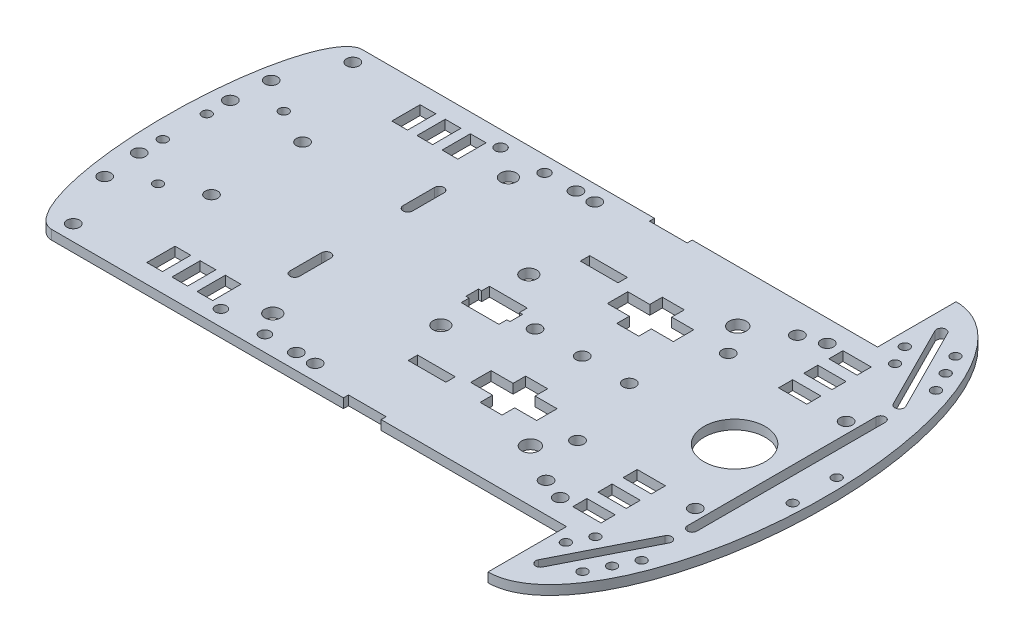
SolidWorks part; units mm, degrees
ref_plane "Front Plane" through (0, 0, 0) normal (0, 0, 1) x (1, 0, 0)
ref_plane "Top Plane" through (0, 0, 0) normal (0, 1, 0) x (1, 0, 0)
ref_plane "Right Plane" through (0, 0, 0) normal (1, 0, 0) x (0, 0, -1)
sketch "Sketch1" plane through (0, 0, 0) normal (0, 1, 0) x (1, 0, 0)
  line L1 (0, 0) -> (210, 0)
  line L2 (0, 0) -> (0, 149)
  line L3 (0, 149) -> (210, 149)
  line L4 (210, 0) -> (210, 149)
  dimension "D1" = 210
  dimension "D2" = 149
extrude "Boss-Extrude1" add sketch "Sketch1" along normal blind 3
sketch "Sketch2" plane through (0, 3, 0) normal (0, 1, 0) x (1, 0, 0)
  line L0 (210, 149) -> (0, 149) construction
  line L1 (177, 149) -> (0, 149)
  line L2 (177, 149) -> (177, 124)
  line L3 (177, 124) -> (0, 124)
  line L4 (0, 149) -> (0, 124)
  line L5 (0, 149) -> (0, 0) construction
  line L7 (0, 0) -> (177, 0)
  line L8 (0, 0) -> (0, 25)
  line L9 (0, 25) -> (177, 25)
  line L10 (177, 0) -> (177, 25)
  dimension "D1" = 177
  dimension "D2" = 25
  dimension "D3" = 25
extrude "Cut-Extrude1" cut sketch "Sketch2" against normal blind 3
sketch "Sketch3" plane through (0, 3, 0) normal (0, 1, 0) x (1, 0, 0)
  line L0 (0, 124) -> (177, 124) construction
  line L1 (143, 99.5) -> (122, 99.5)
  line L2 (143, 99.5) -> (143, 93)
  line L3 (143, 93) -> (122, 93)
  line L4 (122, 99.5) -> (122, 93)
  line L5 (129, 103.5) -> (136, 103.5)
  line L6 (129, 103.5) -> (129, 89)
  line L7 (129, 89) -> (136, 89)
  line L8 (136, 103.5) -> (136, 89)
  line L9 (177, 124) -> (177, 149) construction
  line L10 (118, 124) -> (106, 124)
  line L11 (118, 124) -> (118, 122.4)
  line L12 (118, 122.4) -> (106, 122.4)
  line L13 (106, 124) -> (106, 122.4)
  line L14 (210, 74.5) -> (0, 74.5) construction
  line L15 (118, 103.4) -> (106, 103.4)
  line L16 (118, 103.4) -> (118, 100.4)
  line L17 (118, 100.4) -> (106, 100.4)
  line L18 (106, 103.4) -> (106, 100.4)
  line L19 (181.5, 117.5) -> (172.5, 117.5)
  line L20 (181.5, 117.5) -> (181.5, 113)
  line L21 (181.5, 113) -> (172.5, 113)
  line L22 (172.5, 117.5) -> (172.5, 113)
  line L23 (172.5, 109.5) -> (181.5, 109.5)
  line L24 (172.5, 109.5) -> (172.5, 105)
  line L25 (172.5, 105) -> (181.5, 105)
  line L26 (181.5, 109.5) -> (181.5, 105)
  line L27 (172.5, 101.5) -> (181.5, 101.5)
  line L28 (172.5, 101.5) -> (172.5, 97)
  line L29 (172.5, 97) -> (181.5, 97)
  line L30 (181.5, 101.5) -> (181.5, 97)
  line L31 (210, 0) -> (210, 149) construction
  line L32 (0, 124) -> (0, 25) construction
  line L33 (181.5, 47.5) -> (181.5, 52)
  line L34 (172.5, 52) -> (181.5, 52)
  line L35 (172.5, 47.5) -> (172.5, 52)
  line L36 (172.5, 47.5) -> (181.5, 47.5)
  line L37 (181.5, 39.5) -> (181.5, 44)
  line L38 (172.5, 44) -> (181.5, 44)
  line L39 (172.5, 39.5) -> (172.5, 44)
  line L40 (172.5, 39.5) -> (181.5, 39.5)
  line L41 (172.5, 31.5) -> (172.5, 36)
  line L42 (181.5, 36) -> (172.5, 36)
  line L43 (181.5, 31.5) -> (181.5, 36)
  line L44 (181.5, 31.5) -> (172.5, 31.5)
  line L45 (106, 45.6) -> (106, 48.6)
  line L46 (118, 48.6) -> (106, 48.6)
  line L47 (118, 45.6) -> (118, 48.6)
  line L48 (118, 45.6) -> (106, 45.6)
  line L49 (106, 25) -> (106, 26.6)
  line L50 (118, 26.6) -> (106, 26.6)
  line L51 (118, 25) -> (118, 26.6)
  line L52 (118, 25) -> (106, 25)
  line L53 (136, 45.5) -> (136, 60)
  line L54 (129, 60) -> (136, 60)
  line L55 (129, 45.5) -> (129, 60)
  line L56 (129, 45.5) -> (136, 45.5)
  line L57 (122, 49.5) -> (122, 56)
  line L58 (143, 56) -> (122, 56)
  line L59 (143, 49.5) -> (143, 56)
  line L60 (143, 49.5) -> (122, 49.5)
  circle A0 centre (149, 107.5) radius 2.75
  circle A1 centre (168, 117) radius 2
  circle A2 centre (161, 114.5) radius 2
  circle A3 centre (155, 98.5) radius 2
  circle A4 centre (155, 50.5) radius 2
  circle A5 centre (161, 34.5) radius 2
  circle A6 centre (168, 32) radius 2
  circle A7 centre (149, 41.5) radius 2.75
  dimension "D16" = 5.5
  dimension "D19" = 9
  dimension "D21" = 4
  dimension "D25" = 4
  dimension "D27" = 4
  dimension "D1" = 34
  dimension "D2" = 6.5
  dimension "D3" = 24.5
  dimension "D4" = 21
  dimension "D5" = 7
  dimension "D6" = 7
  dimension "D7" = 4
  dimension "D8" = 4
  dimension "D9" = 59
  dimension "D10" = 12
  dimension "D11" = 1.6
  dimension "D12" = 3
  dimension "D13" = 19
  dimension "D14" = 12
  dimension "D15" = 59
  dimension "D17" = 28
  dimension "D18" = 16.5
  dimension "D20" = 7
  dimension "D22" = 16
  dimension "D23" = 9.5
  dimension "D24" = 25.5
  dimension "D26" = 22
  dimension "D28" = 4.5
  dimension "D29" = 9
  dimension "D30" = 4.5
  dimension "D31" = 6.5
  dimension "D32" = 4.5
  dimension "D33" = 3.5
  dimension "D34" = 9
  dimension "D35" = 4.5
  dimension "D36" = 3.5
extrude "Cut-Extrude2" cut sketch "Sketch3" against normal blind 3 contours L15 L18 L17 L16 | L6 L1 L4 L3 | L8 L1 L6 L3 | L1 L8 L3 L2 | L8 L3 L6 L7 | L8 L5 L6 L1 | A3 | A0 | A2 | A1 | L19 L22 L21 L20 | L26 L23 L24 L25 | L30 L27 L28 L29 | L48 L47 L46 L45 | L10 L13 L12 L11 | L50 L49 L52 L51 | L55 L54 L53 L56 | L58 L57 L60 L59 | A7 | A4 | A5 | A6 | L34 L33 L36 L35 | L38 L37 L40 L39 | L42 L41 L44 L43
sketch "Sketch4" plane through (0, 3, 0) normal (0, 1, 0) x (1, 0, 0)
  line L0 (0, 124) -> (106, 124) construction
  line L1 (106, 124) -> (106, 122.4) construction
  line L2 (106, 124) -> (106, 122.4) construction
  line L3 (210, 74.5) -> (0, 74.5) construction
  line L4 (210, 0) -> (210, 149) construction
  line L5 (0, 124) -> (0, 25) construction
  circle A0 centre (92, 119) radius 2
  circle A1 centre (86, 119) radius 2
  circle A2 centre (76, 119) radius 1.75
  circle A3 centre (62, 119) radius 1.75
  circle A4 centre (71.5, 112) radius 2.5
  circle A5 centre (71.5, 37) radius 2.5
  circle A6 centre (62, 30) radius 1.75
  circle A7 centre (76, 30) radius 1.75
  circle A8 centre (86, 30) radius 2
  circle A9 centre (92, 30) radius 2
  circle A10 centre (15, 119) radius 2
  circle A11 centre (15, 30) radius 2
  point P11 (106, 123.2)
  point P16 (106, 123.2)
  dimension "D1" = 4
  dimension "D2" = 4
  dimension "D6" = 5
  dimension "D8" = 3.5
  dimension "D12" = 3.5
  dimension "D13" = 5
  dimension "D17" = 4
  dimension "D3" = 6
  dimension "D4" = 14
  dimension "D5" = 5
  dimension "D7" = 30
  dimension "D9" = 5
  dimension "D10" = 14
  dimension "D11" = 5
  dimension "D14" = 34.5
  dimension "D15" = 12
  dimension "D16" = 47
  dimension "D18" = 5
extrude "Cut-Extrude3" cut sketch "Sketch4" against normal blind 3
sketch "Sketch5" plane through (0, 3, 0) normal (0, 1, 0) x (1, 0, 0)
  line L0 (0, 124) -> (106, 124) construction
  line L1 (58.4, 118) -> (53.4, 118)
  line L2 (58.4, 118) -> (58.4, 109)
  line L3 (58.4, 109) -> (53.4, 109)
  line L4 (53.4, 118) -> (53.4, 109)
  line L5 (0, 74.5) -> (210, 74.5) construction
  line L6 (50.4, 118) -> (45.4, 118)
  line L7 (50.4, 118) -> (50.4, 109)
  line L8 (50.4, 109) -> (45.4, 109)
  line L9 (45.4, 118) -> (45.4, 109)
  line L10 (42.4, 118) -> (37.4, 118)
  line L11 (42.4, 118) -> (42.4, 109)
  line L12 (42.4, 109) -> (37.4, 109)
  line L13 (37.4, 118) -> (37.4, 109)
  line L14 (0, 124) -> (0, 25) construction
  line L15 (210, 0) -> (210, 149) construction
  line L16 (37.4, 31) -> (37.4, 40)
  line L17 (42.4, 40) -> (37.4, 40)
  line L18 (42.4, 31) -> (42.4, 40)
  line L19 (42.4, 31) -> (37.4, 31)
  line L20 (45.4, 31) -> (45.4, 40)
  line L21 (50.4, 40) -> (45.4, 40)
  line L22 (50.4, 31) -> (50.4, 40)
  line L23 (50.4, 31) -> (45.4, 31)
  line L24 (53.4, 31) -> (53.4, 40)
  line L25 (58.4, 40) -> (53.4, 40)
  line L26 (58.4, 31) -> (58.4, 40)
  line L27 (58.4, 31) -> (53.4, 31)
  dimension "D1" = 5
  dimension "D2" = 9
  dimension "D3" = 47.6
  dimension "D4" = 6
  dimension "D5" = 5
  dimension "D6" = 5
  dimension "D7" = 3
  dimension "D8" = 3
  dimension "D9" = 9
  dimension "D10" = 9
extrude "Cut-Extrude4" cut sketch "Sketch5" against normal blind 3
sketch "Sketch6" plane through (0, 3, 0) normal (0, 1, 0) x (1, 0, 0)
  line L0 (0, 74.5) -> (210, 74.5) construction
  line L1 (0, 124) -> (0, 25) construction
  line L2 (210, 0) -> (210, 149) construction
  line L3 (29, 60) -> (29, 89)
  line L4 (29, 60) -> (6, 60)
  line L5 (29, 89) -> (6, 89)
  line L6 (6, 60) -> (6, 89)
  line L7 (29, 60) -> (6, 89) construction
  line L8 (29, 89) -> (6, 60) construction
  line L9 (0, 74.5) -> (46.1912, 74.5) construction
  circle A0 centre (6, 89) radius 2
  circle A1 centre (29, 89) radius 2
  circle A2 centre (29, 60) radius 2
  circle A3 centre (6, 60) radius 2
  circle A4 centre (6, 81.5) radius 1.5
  circle A5 centre (6, 67.5) radius 1.5
  circle A6 centre (7, 48) radius 2
  circle A7 centre (17.5, 54.5) radius 1.5
  circle A8 centre (17.5, 94.5) radius 1.5
  circle A9 centre (7, 101) radius 2
  point P7 (17.5, 74.5)
  dimension "D4" = 4
  dimension "D5" = 4
  dimension "D6" = 4
  dimension "D7" = 4
  dimension "D8" = 3
  dimension "D9" = 3
  dimension "D12" = 12
  dimension "D14" = 20
  dimension "D1" = 29
  dimension "D2" = 23
  dimension "D3" = 6
  dimension "D10" = 14
  dimension "D11" = 7
  dimension "D13" = 1
sketch "Sketch7" plane through (0, 3, 0) normal (0, 1, 0) x (1, 0, 0)
  line L0 (0, 74.5) -> (210, 74.5) construction
  line L1 (210, 0) -> (210, 149) construction
  line L2 (172.5, 101.5) -> (172.5, 97) construction
  line L3 (106, 103.4) -> (106, 100.4) construction
  line L4 (98.5, 79) -> (110.5, 79)
  line L5 (98.5, 79) -> (98.5, 70)
  line L6 (98.5, 70) -> (110.5, 70)
  line L7 (110.5, 79) -> (110.5, 70)
  line L8 (97.5, 76.5) -> (111.5, 76.5)
  line L9 (97.5, 76.5) -> (97.5, 72.5)
  line L10 (97.5, 72.5) -> (111.5, 72.5)
  line L11 (111.5, 76.5) -> (111.5, 72.5)
  line L12 (77.2099, 74.5) -> (123.0417, 74.5) construction
  circle A0 centre (181, 74.5) radius 9.75
  circle A1 centre (132.5, 74.5) radius 2
  circle A2 centre (147.5, 74.5) radius 2
  circle A3 centre (117.5, 74.5) radius 2
  circle A4 centre (101.5, 88.5) radius 2.5
  circle A5 centre (101.5, 60.5) radius 2.5
  point P6 (172.5, 99.25)
  point P28 (106, 101.9)
  dimension "D1" = 19.5
  dimension "D3" = 15
  dimension "D16" = 5
  dimension "D2" = 29
  dimension "D4" = 15
  dimension "D5" = 3.5
  dimension "D6" = 9
  dimension "D7" = 4.5
  dimension "D8" = 12
  dimension "D9" = 14
  dimension "D10" = 4
  dimension "D11" = 2
  dimension "D12" = 1
  dimension "D13" = 6
  dimension "D14" = 14
  dimension "D15" = 4.5
extrude "Cut-Extrude5" cut sketch "Sketch7" against normal blind 3 contours A4 | A5 | L10 L5 L6 L7 | A3 | A1 | A2 | A0
extrude "Cut-Extrude6" cut sketch "Sketch6" against normal blind 3 contours A9 | A8 | A0 | A1 | A2 | A4 | A5 | A3 | A7 | A6
sketch "Sketch8" plane through (0, 3, 0) normal (0, 1, 0) x (1, 0, 0)
  line L0 (64, 97.5) -> (64, 87.5) construction
  line L1 (65.5, 97.5) -> (65.5, 87.5)
  line L2 (62.5, 97.5) -> (62.5, 87.5)
  line L3 (0, 74.5) -> (210, 74.5) construction
  line L4 (0, 124) -> (0, 25) construction
  line L5 (210, 0) -> (210, 149) construction
  line L6 (0, 124) -> (106, 124) construction
  line L7 (98.5, 79) -> (98.5, 76.5) construction
  line L8 (36.7858, 74.5) -> (83.2541, 74.5) construction
  line L9 (64, 51.5) -> (64, 61.5) construction
  line L10 (65.5, 51.5) -> (65.5, 61.5)
  line L11 (62.5, 51.5) -> (62.5, 61.5)
  arc A0 (65.5, 97.5) -> (62.5, 97.5) centre (64, 97.5) ccw
  arc A1 (62.5, 87.5) -> (65.5, 87.5) centre (64, 87.5) ccw
  circle A2 centre (29, 89) radius 2 construction
  arc A3 (65.5, 51.5) -> (62.5, 51.5) centre (64, 51.5) cw
  arc A4 (62.5, 61.5) -> (65.5, 61.5) centre (64, 61.5) cw
  point P2 (64, 92.5)
  point P17 (98.5, 77.75)
  point P24 (64, 56.5)
  dimension "D1" = 1.5
  dimension "D2" = 10
  dimension "D3" = 13
  dimension "D4" = 26.5
  dimension "D5" = 35
  dimension "D6" = 34.5
extrude "Cut-Extrude7" cut sketch "Sketch8" against normal blind 3
sketch "Sketch9" plane through (0, 3, 0) normal (0, 1, 0) x (1, 0, 0)
  line L0 (210, 74.5) -> (157.0079, 74.5) construction
  line L1 (210, 0) -> (210, 149) construction
  line L2 (197.5, 104.5) -> (197.5, 44.5) construction
  line L3 (199, 104.5) -> (199, 44.5)
  line L4 (196, 104.5) -> (196, 44.5)
  line L5 (196.5, 111.5) -> (183, 138.2909) construction
  line L6 (195.1605, 110.825) -> (181.6605, 137.6159)
  line L7 (197.8395, 112.175) -> (184.3395, 138.9659)
  line L8 (177, 124) -> (177, 149) construction
  line L9 (195.1082, 127.5954) -> (189.75, 124.8954) construction
  line L10 (183, 138.2909) -> (196.5, 111.5) construction
  line L11 (191.9582, 133.8466) -> (195.1082, 127.5954) construction
  line L12 (195.1082, 127.5954) -> (200.2073, 117.4762) construction
  line L13 (195.1082, 127.5954) -> (189.75, 124.8954) construction
  line L14 (189.75, 124.8954) -> (183, 121.4941) construction
  line L15 (191.9582, 133.8466) -> (180.4567, 128.051) construction
  line L16 (196.5, 37.5) -> (183, 10.7091) construction
  line L17 (195.1605, 38.175) -> (181.6605, 11.3841)
  line L18 (197.8395, 36.825) -> (184.3395, 10.0341)
  arc A0 (199, 104.5) -> (196, 104.5) centre (197.5, 104.5) ccw
  arc A1 (196, 44.5) -> (199, 44.5) centre (197.5, 44.5) ccw
  circle A2 centre (181, 74.5) radius 9.75 construction
  arc A3 (195.1605, 110.825) -> (197.8395, 112.175) centre (196.5, 111.5) ccw
  arc A4 (184.3395, 138.9659) -> (181.6605, 137.6159) centre (183, 138.2909) ccw
  circle A5 centre (195.1082, 127.5954) radius 1.5
  circle A6 centre (191.9582, 133.8466) radius 1.5
  circle A7 centre (198.2582, 121.3442) radius 1.5
  circle A8 centre (184.3918, 122.1954) radius 1.5
  circle A9 centre (181.2418, 128.4466) radius 1.5
  circle A10 centre (192.5, 98.5) radius 2
  circle A11 centre (206.5, 81.5) radius 1.5
  circle A12 centre (192.5, 50.5) radius 2
  circle A13 centre (184.3918, 26.8046) radius 1.5
  circle A14 centre (181.2418, 20.5534) radius 1.5
  circle A15 centre (191.9582, 15.1534) radius 1.5
  circle A16 centre (195.1082, 21.4046) radius 1.5
  circle A17 centre (198.2582, 27.6558) radius 1.5
  arc A18 (195.1605, 38.175) -> (197.8395, 36.825) centre (196.5, 37.5) cw
  arc A19 (184.3395, 10.0341) -> (181.6605, 11.3841) centre (183, 10.7091) cw
  circle A20 centre (206.5, 67.5) radius 1.5
  point P6 (197.5, 74.5)
  point P15 (189.75, 124.8954)
  point P56 (189.75, 24.1046)
  dimension "D4" = 15
  dimension "D3" = 1.5
  dimension "D9" = 1.5
  dimension "D10" = 3
  dimension "D14" = 3
  dimension "D18" = 6
  dimension "D16" = 3
  dimension "D17" = 3
  dimension "D19" = 6
  dimension "D20" = 3
  dimension "D23" = 4
  dimension "D25" = 3
  dimension "D1" = 60
  dimension "D2" = 30
  dimension "D5" = 30
  dimension "D6" = 1
  dimension "D7" = 7
  dimension "D8" = 6
  dimension "D11" = 6
  dimension "D12" = 7
  dimension "D13" = 6
  dimension "D15" = 7
  dimension "D21" = 24
  dimension "D22" = 5
  dimension "D24" = 7
  dimension "D26" = 9
extrude "Cut-Extrude8" cut sketch "Sketch9" against normal blind 3
sketch "Sketch11" plane through (0, 3, 0) normal (0, 1, 0) x (1, 0, 0)
  line L0 (210, 0) -> (210, 149) construction
  line L1 (177, 149) -> (210, 149)
  line L2 (210, 149) -> (210, 0)
  line L3 (210, 0) -> (177, 0)
  ellipse E0 centre (177, 74.5) end of major axis (177, 149) minor radius 33
extrude "Cut-Extrude9" cut sketch "Sketch11" against normal blind 3 contours E0 L2 L1 | E0 L3 L2
sketch "Sketch12" plane through (0, 3, 0) normal (0, 1, 0) x (1, 0, 0)
  line L0 (0, 124) -> (106, 124) construction
  line L1 (13, 124) -> (0, 124)
  line L2 (0, 124) -> (0, 74.5)
  line L3 (0, 124) -> (0, 25) construction
  line L4 (0, 74.5) -> (0, 25)
  line L5 (0, 25) -> (13, 25)
  ellipse E0 centre (13, 74.5) end of major axis (13, 124) minor radius 13
  dimension "D1" = 13
extrude "Cut-Extrude10" cut sketch "Sketch12" against normal blind 3 contours E0 L1 L2 | E0 L4 L5
